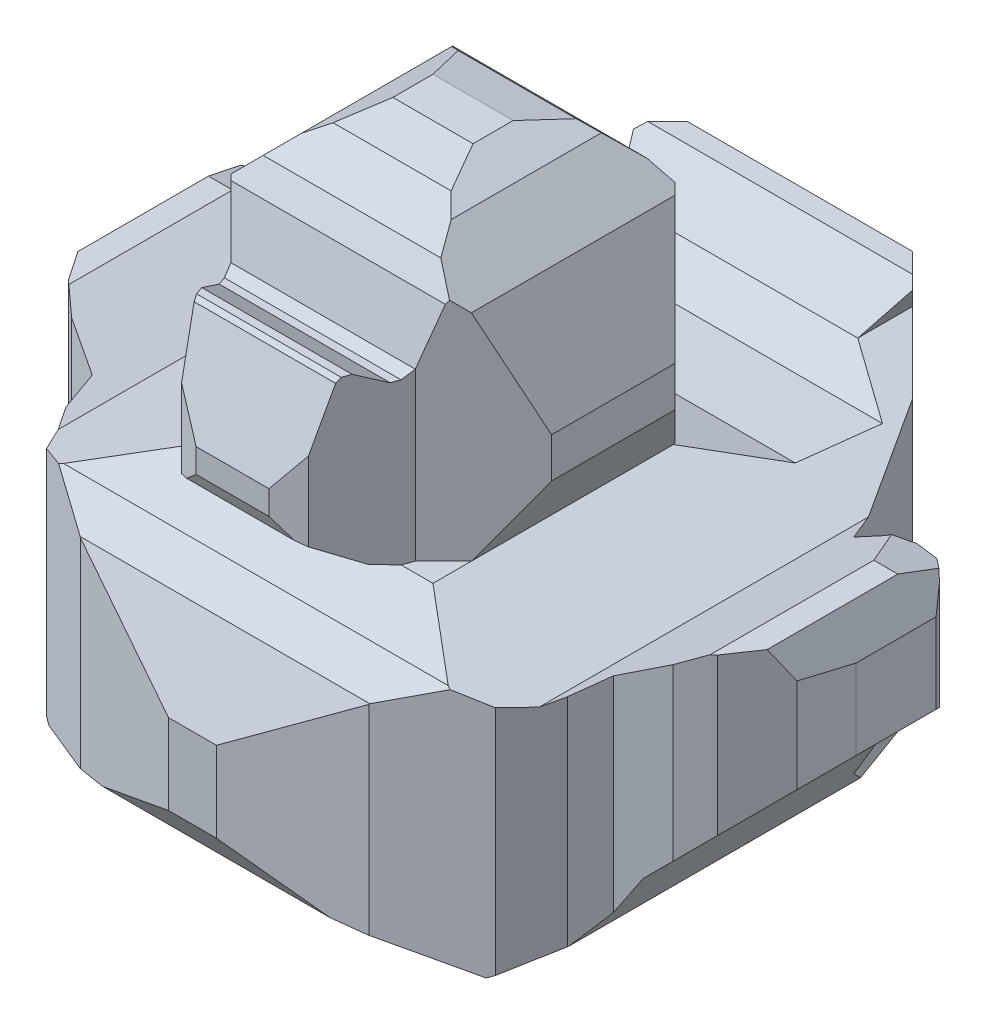
SolidWorks part; units mm, degrees
ref_plane "Front Plane" through (0, 0, 0) normal (0, 0, 1) x (1, 0, 0)
ref_plane "Top Plane" through (0, 0, 0) normal (0, 1, 0) x (1, 0, 0)
ref_plane "Right Plane" through (0, 0, 0) normal (1, 0, 0) x (0, 0, -1)
sketch "Sketch1" plane through (0, 0, 0) normal (0, 0, 1) x (1, 0, 0)
  line L0 (1.25, 0) -> (-1.25, 0)
  line L2 (-1.75, 0.5) -> (-2.25, 1)
  line L3 (-2.25, 1) -> (-2.25, 1.5)
  line L5 (-2, 1.75) -> (-1.5, 1.5)
  line L6 (-1.5, 1.5) -> (-0.75, 1.75)
  line L7 (-0.75, 1.75) -> (-1, 2.183)
  line L8 (-1, 2.183) -> (-1, 2.433)
  line L9 (-1, 2.433) -> (-0.75, 3.0915)
  line L10 (-0.75, 3.0915) -> (-0.4665, 3.375)
  line L11 (-0.4665, 3.375) -> (-0.25, 3.5)
  line L12 (-0.25, 3.5) -> (0.25, 3.5)
  line L13 (0, 3.5) -> (0, 0) construction
  line L14 (-1.25, 0) -> (-1.567, 0.183)
  line L15 (-1.567, 0.183) -> (-1.75, 0.5)
  line L16 (-2, 1.75) -> (-2.15, 1.75)
  line L17 (-2.15, 1.75) -> (-2.25, 1.5)
  line L18 (2.15, 1.75) -> (2.25, 1.5)
  line L19 (2, 1.75) -> (2.15, 1.75)
  line L20 (1.567, 0.183) -> (1.75, 0.5)
  line L21 (1.25, 0) -> (1.567, 0.183)
  line L22 (0.4665, 3.375) -> (0.25, 3.5)
  line L23 (0.75, 3.0915) -> (0.4665, 3.375)
  line L24 (1, 2.433) -> (0.75, 3.0915)
  line L25 (1, 2.183) -> (1, 2.433)
  line L26 (0.75, 1.75) -> (1, 2.183)
  line L27 (1.5, 1.5) -> (0.75, 1.75)
  line L28 (2, 1.75) -> (1.5, 1.5)
  line L29 (2.25, 1) -> (2.25, 1.5)
  line L30 (1.75, 0.5) -> (2.25, 1)
  point P13 (0, 0)
  point P16 (0, 0)
  point P17 (-1.5, 1.4084)
  dimension "D1" = 2.25
  dimension "D2" = 1.25
  dimension "D3" = 0.1
  dimension "D4" = 0.5
  dimension "D5" = 0.5
  dimension "D6" = 3.5
  dimension "D7" = 1
  dimension "D8" = 0.75
  dimension "D9" = 1.75
  dimension "D10" = 0.5
  dimension "D11" = 150
  dimension "D12" = 0.25
  dimension "D13" = 0.25
  dimension "D14" = 135
  dimension "D15" = 0.25
  dimension "D16" = 0.5
  dimension "D17" = 0.5
  dimension "D18" = 0.15
  dimension "D19" = 150
  dimension "D20" = 1.5
extrude "Boss-Extrude1" add sketch "Sketch1" against normal blind 4
sketch "Sketch2" plane through (0, 0, 0) normal (0, 1, 0) x (1, 0, 0)
  line L0 (-2.25, 4) -> (-0.125, 4)
  line L1 (2.25, 4) -> (2.25, 2.3881)
  line L2 (2.25, 0) -> (0.15, 0)
  line L3 (-2.25, 0) -> (-2.25, 1.8881)
  line L4 (0, 0) -> (0, 4) construction
  line L5 (-2.25, 2.3881) -> (-2.25, 4)
  line L6 (-0.125, 4) -> (-0.625, 3.866)
  line L7 (-0.625, 3.866) -> (-1.125, 3.366)
  line L8 (-1.125, 3.366) -> (-1.375, 2.933)
  line L9 (-1.375, 2.933) -> (-1.625, 2.5)
  line L10 (-1.625, 2.5) -> (-1.8, 2.5153)
  line L11 (-1.8, 2.5153) -> (-1.95, 2.5699)
  line L12 (-1.95, 2.5699) -> (-2.1, 2.5435)
  line L13 (-2.1, 2.5435) -> (-2.2, 2.4595)
  line L14 (-2.2, 2.4595) -> (-2.25, 2.3881)
  line L15 (-2.25, 1.8881) -> (-2.225, 1.5453)
  line L16 (-2.225, 1.5453) -> (-2.025, 1.2506)
  line L17 (-2.025, 1.2506) -> (-1.875, 1.121)
  line L18 (-1.875, 1.121) -> (-1.625, 1)
  line L20 (-2.25, 4) -> (-2.25, 0) construction
  line L21 (-1.625, 1) -> (-1.5647, 0.7749)
  line L22 (-1.5647, 0.7749) -> (-1.4, 0.4896)
  line L23 (-1.4, 0.4896) -> (-0.9, 0.201)
  line L24 (-0.9, 0.201) -> (-0.15, 0)
  line L26 (0.125, 4) -> (0.625, 3.866)
  line L27 (0.9, 0.201) -> (0.15, 0)
  line L28 (1.4, 0.4896) -> (0.9, 0.201)
  line L29 (1.5647, 0.7749) -> (1.4, 0.4896)
  line L30 (1.625, 1) -> (1.5647, 0.7749)
  line L31 (1.875, 1.121) -> (1.625, 1)
  line L32 (2.025, 1.2506) -> (1.875, 1.121)
  line L33 (2.225, 1.5453) -> (2.025, 1.2506)
  line L34 (2.25, 1.8881) -> (2.225, 1.5453)
  line L35 (2.2, 2.4595) -> (2.25, 2.3881)
  line L36 (2.1, 2.5435) -> (2.2, 2.4595)
  line L37 (1.95, 2.5699) -> (2.1, 2.5435)
  line L38 (1.8, 2.5153) -> (1.95, 2.5699)
  line L39 (1.625, 2.5) -> (1.8, 2.5153)
  line L40 (1.375, 2.933) -> (1.625, 2.5)
  line L41 (1.125, 3.366) -> (1.375, 2.933)
  line L42 (0.625, 3.866) -> (1.125, 3.366)
  line L43 (0.125, 4) -> (2.25, 4)
  line L44 (-0.15, 0) -> (-2.25, 0)
  line L45 (2.25, 1.8881) -> (2.25, 0)
  point P17 (-1.5, 0.7086)
  point P32 (-1.5722, 0.7831)
  point P33 (-1.409, 0.4816)
  point P35 (-1.5, 0.7725)
  dimension "D1" = 1.5
  dimension "D2" = 165
  dimension "D3" = 0.125
  dimension "D4" = 150
  dimension "D5" = 0.5
  dimension "D6" = 0.5
  dimension "D7" = 1.625
  dimension "D8" = 0.25
  dimension "D9" = 0.05
  dimension "D10" = 0.1
  dimension "D11" = 0.15
  dimension "D12" = 0.15
  dimension "D13" = 165
  dimension "D14" = 115
  dimension "D15" = 165
  dimension "D16" = 150
  dimension "D17" = 150
  dimension "D18" = 165
  dimension "D19" = 3
  dimension "D20" = 150
  dimension "D21" = 345
  dimension "D22" = 165
  dimension "D23" = 0.25
  dimension "D24" = 0.15
  dimension "D25" = 0.2
  dimension "D26" = 0.5
  dimension "D27" = 165
  dimension "D28" = 165
  dimension "D29" = 150
  dimension "D30" = 165
  dimension "D31" = 0.15
  dimension "D32" = 0.75
  dimension "D33" = 0.5
extrude "Cut-Extrude2" cut sketch "Sketch2" against normal through all and the other way through all
sketch "Sketch3" plane through (0, 0, 0) normal (1, 0, 0) x (0, 0, -1)
  line L0 (0.75, 0) -> (0.5, 0.05)
  line L1 (3.1495, 0) -> (0.403, 0) construction
  line L2 (0.5, 0.05) -> (0.15, 0.2231)
  line L3 (0.15, 0.2231) -> (0, 0.4481)
  line L4 (0, 3.5) -> (0, 0) construction
  line L5 (0, 0.4481) -> (0, 0)
  line L6 (0, 0) -> (0.75, 0)
  line L7 (0.75, 1.75) -> (0.3953, 1.6)
  line L8 (3.741, 1.75) -> (0.1608, 1.75) construction
  line L9 (0.3953, 1.6) -> (0.2028, 1.45)
  line L10 (0.2028, 1.45) -> (0, 0.95)
  line L11 (0.75, 1.75) -> (0.6, 1.8004)
  line L12 (0.6, 1.8004) -> (0.3, 1.9994)
  line L13 (0.3, 1.9994) -> (0.25, 2.1)
  line L14 (0.25, 2.1) -> (0.25, 2.25)
  line L19 (0.4518, 2.825) -> (0.4768, 2.85)
  line L20 (0.4768, 2.85) -> (0.5268, 2.85)
  line L21 (0.5268, 2.85) -> (0.7, 2.75)
  line L22 (0.7, 2.75) -> (0.75, 2.75)
  line L23 (0.75, 2.75) -> (0.8147, 2.7874)
  line L24 (0.8147, 2.7874) -> (0.9085, 3.1374)
  line L25 (0.9085, 3.1374) -> (0.9951, 3.2874)
  line L26 (0.9951, 3.2874) -> (1.2451, 3.4317)
  line L27 (1.2451, 3.4317) -> (1.5, 3.5)
  line L28 (3.9665, 3.5) -> (0.0268, 3.5) construction
  line L29 (1.5, 3.5) -> (0, 3.5)
  line L30 (0, 3.5) -> (0, 0.95)
  line L31 (1.75, 3.5) -> (2.025, 3.4317)
  line L32 (2.025, 3.4317) -> (2.229, 3.235)
  line L33 (2.229, 3.235) -> (2.3752, 2.9923)
  line L34 (2.3752, 2.9923) -> (2.5, 2.5584)
  line L35 (2.5, 2.5584) -> (2.5046, 2.3084)
  line L36 (2.5046, 2.3084) -> (2.4603, 2.1303)
  line L37 (2.4603, 2.1303) -> (2.25, 1.75)
  line L38 (2.5015, 1.75) -> (1.4348, 1.75) construction
  line L39 (2.25, 1.75) -> (2.65, 1.6301)
  line L40 (2.65, 1.6301) -> (3.15, 1.6153)
  line L41 (3.15, 1.6153) -> (3.4, 1.75)
  line L42 (3.4, 1.75) -> (3.6652, 2)
  line L43 (3.2578, 0) -> (4, 0)
  line L44 (3.6652, 2) -> (3.7887, 2)
  line L45 (3.7887, 2) -> (3.933, 1.75)
  line L46 (3.933, 1.75) -> (4, 1.5)
  line L47 (4, 3.5) -> (4, 0) construction
  line L48 (4, 1.5) -> (4, 3.5)
  line L49 (4, 3.5) -> (1.75, 3.5)
  line L50 (4, 1.25) -> (3.8765, 0.75)
  line L51 (3.8765, 0.75) -> (3.7386, 0.5)
  line L52 (3.7386, 0.5) -> (3.2578, 0)
  line L53 (3.1495, 0) -> (3.366, 0) construction
  line L54 (4, 0) -> (4, 1.25)
  line L55 (0.4518, 2.825) -> (0.25, 2.25)
  point P19 (0, 0)
  point P24 (0, 0)
  dimension "D1" = 0.75
  dimension "D2" = 165
  dimension "D3" = 150
  dimension "D4" = 0.25
  dimension "D5" = 0.35
  dimension "D6" = 0.05
  dimension "D7" = 165
  dimension "D8" = 0.75
  dimension "D9" = 150
  dimension "D10" = 0.15
  dimension "D11" = 0.15
  dimension "D12" = 0.5
  dimension "D13" = 165
  dimension "D14" = 150
  dimension "D15" = 0.5
  dimension "D16" = 0.15
  dimension "D17" = 0.3
  dimension "D18" = 0.575
  dimension "D19" = 135
  dimension "D20" = 0.05
  dimension "D21" = 0.35
  dimension "D23" = 0.15
  dimension "D28" = 0.025
  dimension "D29" = 150
  dimension "D30" = 1
  dimension "D31" = 0.05
  dimension "D32" = 150
  dimension "D33" = 135
  dimension "D34" = 165
  dimension "D35" = 150
  dimension "D36" = 165
  dimension "D37" = 1.5
  dimension "D38" = 0.25
  dimension "D39" = 0.15
  dimension "D40" = 0.35
  dimension "D41" = 2.5
  dimension "D42" = 1.5
  dimension "D43" = 165
  dimension "D44" = 165
  dimension "D45" = 165
  dimension "D46" = 165
  dimension "D47" = 165
  dimension "D48" = 150
  dimension "D49" = 0.25
  dimension "D50" = 0.25
  dimension ".275" = 0.275
  dimension "D51" = 165
  dimension "D52" = 150
  dimension "D53" = 165
  dimension "D54" = 120
  dimension "D55" = 165
  dimension "D56" = 2
  dimension "D57" = 0.4
  dimension "D58" = 0.5
  dimension "D59" = 0.25
  dimension "D60" = 0.25
  dimension "D61" = 0.25
  dimension "D62" = 165
  dimension "D63" = 165
  dimension "D66" = 0.25
  dimension "D67" = 0.5
  dimension "D68" = 0.25
extrude "Cut-Extrude3" cut sketch "Sketch3" against normal through all both and the other way through all
sketch "Sketch4" plane through (0, 3.5, 0) normal (0, 1, 0) x (1, 0, 0)
  line L0 (1, 2.51) -> (0.5, 2.51)
  line L2 (0.5, 2.51) -> (1, 2.01)
  line L3 (1, 2.01) -> (1, 2.51)
  line L4 (-1, 2.51) -> (-0.5, 2.51)
  line L5 (-0.5, 2.51) -> (-1, 2.01)
  line L6 (-1, 2.5023) -> (-1, 0.3142) construction
  line L7 (-1, 2.01) -> (-1, 2.51)
  line L9 (1, 2.5023) -> (1, 0.3142) construction
  line L10 (-0.8655, 0.8147) -> (0.8655, 0.8147) construction
  line L11 (0.575, 0.8147) -> (1, 1.2397)
  line L12 (1, 1.2397) -> (1, 0.2028)
  line L14 (-0.575, 0.8147) -> (-1, 1.2397)
  line L15 (-1, 1.2397) -> (-1, 0.2028)
  line L16 (-0.9524, 2.5) -> (0.9524, 2.5) construction
  line L17 (-0.575, 0.8147) -> (-0.3957, 0.3278)
  line L18 (-0.3957, 0.3278) -> (-0.125, 0.2028)
  line L19 (-0.9032, 0.2028) -> (0.9032, 0.2028) construction
  line L21 (0.125, 0.2028) -> (0.3957, 0.3278)
  line L22 (0.3957, 0.3278) -> (0.575, 0.8147)
  line L23 (-1, 0.2028) -> (-0.125, 0.2028)
  line L24 (1, 0.2028) -> (0.125, 0.2028)
  point P2 (-0.4212, 0.3415)
  point P3 (-0.401, 0.3324)
  point P27 (0, 0)
  point P28 (0, 0.2028)
  dimension "D1" = 0.5
  dimension "D2" = 0.01
  dimension "D3" = 1.15
  dimension "D4" = 0.25
  dimension "D5" = 135
  dimension "D6" = 0.125
  dimension "D7" = 0.125
extrude "Cut-Extrude4" cut sketch "Sketch4" against normal up to vertex (1.75 mm away)
